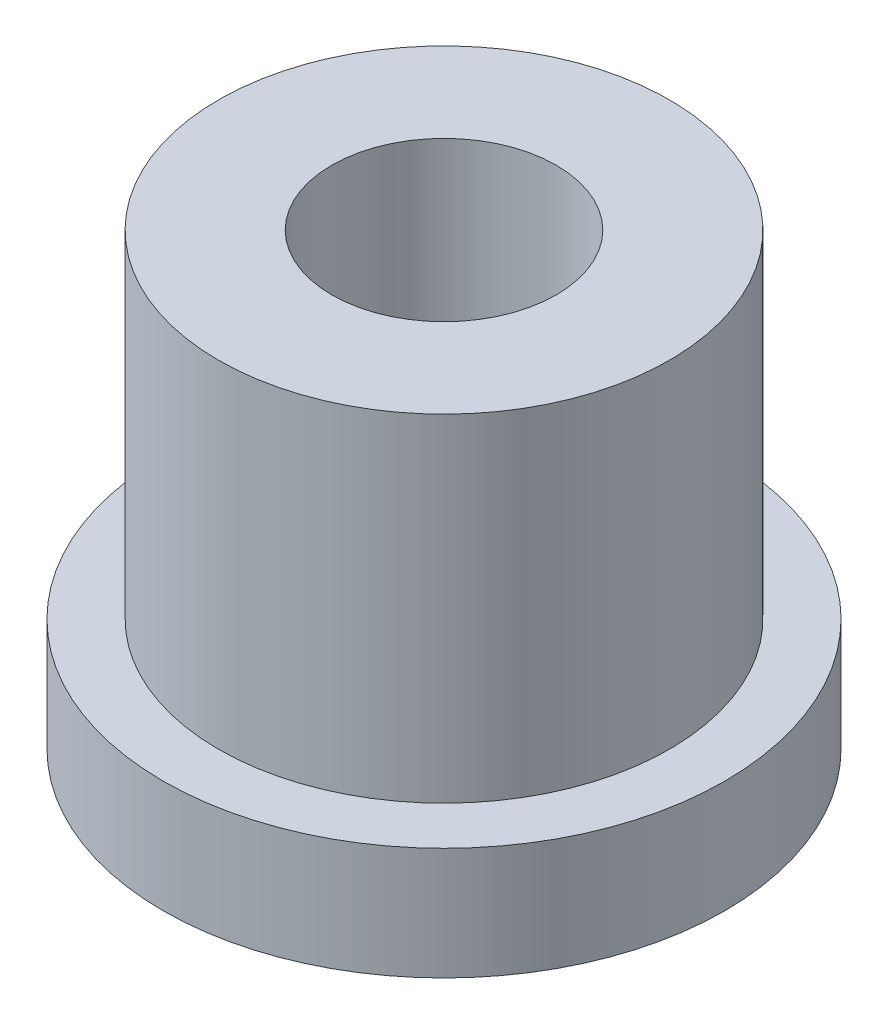
SolidWorks part; units mm, degrees
material "Bronze busing"
ref_plane "Front" through (0, 0, 0) normal (0, 0, 1) x (1, 0, 0)
ref_plane "Top" through (0, 0, 0) normal (0, 1, 0) x (1, 0, 0)
ref_plane "Right" through (0, 0, 0) normal (1, 0, 0) x (0, 0, -1)
sketch "Sketch1" plane through (0, 0, 0) normal (0, 1, 0) x (1, 0, 0)
  circle A0 centre (0, 0) radius 1.5875
  circle A1 centre (0, 0) radius 3.1877
  circle A2 centre (0, 0) radius 3.9688
  dimension "ID" = 3.175
  dimension "OD" = 6.3754
  dimension "FlangeOD" = 7.9375
sketch "Sketch2" plane through (0, 0, 0) normal (0, 1, 0) x (1, 0, 0)
  circle A0 centre (0, 0) radius 1.5875 construction
  circle A1 centre (0, 0) radius 3.1877 construction
  circle A2 centre (0, 0) radius 1.5875
  circle A3 centre (0, 0) radius 3.1877
extrude "Boss-Extrude1" add sketch "Sketch2" along normal blind 6.35
sketch "Sketch3" plane through (0, 0, 0) normal (0, 1, 0) x (1, 0, 0)
  circle A0 centre (0, 0) radius 3.9688 construction
  circle A1 centre (0, 0) radius 3.1877 construction
  circle A2 centre (0, 0) radius 3.9688
  circle A3 centre (0, 0) radius 3.1877
extrude "Boss-Extrude2" add sketch "Sketch3" along normal blind 1.5875
